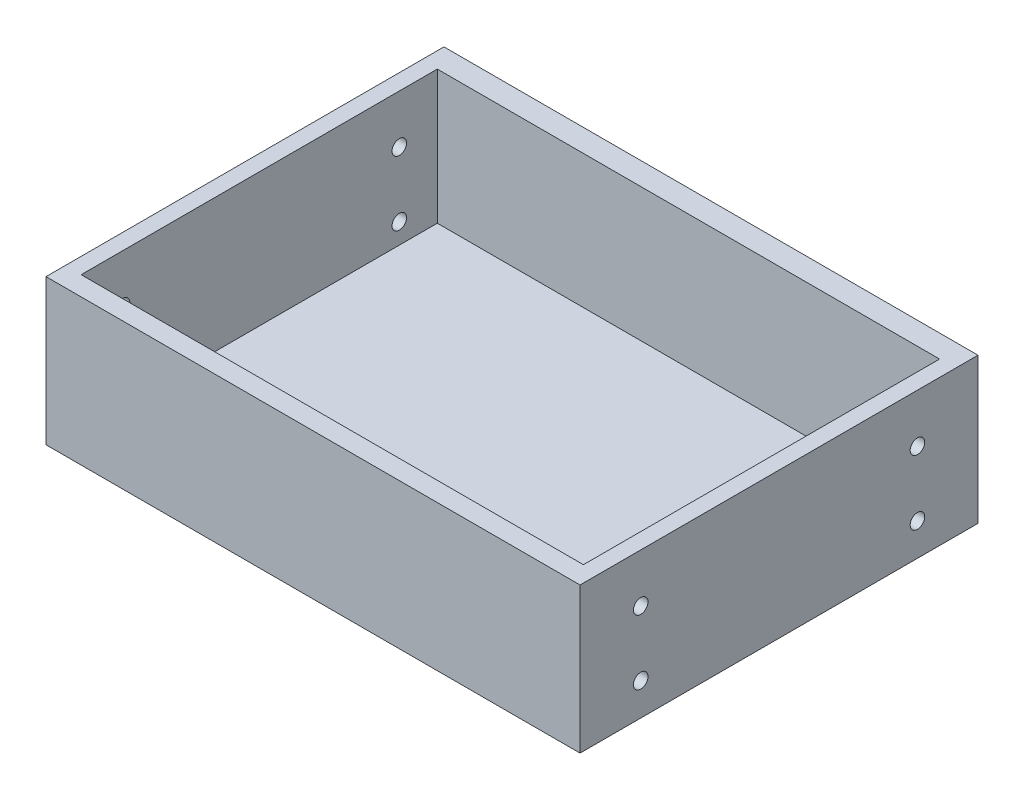
SolidWorks part; units mm, degrees
ref_plane "Front Plane" through (0, 0, 0) normal (0, 0, 1) x (1, 0, 0)
ref_plane "Top Plane" through (0, 0, 0) normal (0, 1, 0) x (1, 0, 0)
ref_plane "Right Plane" through (0, 0, 0) normal (1, 0, 0) x (0, 0, -1)
sketch "Sketch1" plane through (0, 0, 0) normal (0, 1, 0) x (1, 0, 0)
  line L1 (0, 0) -> (-440, 0)
  line L2 (0, 0) -> (0, 327.8893)
  line L3 (0, 327.8893) -> (-440, 327.8893)
  line L4 (-440, 0) -> (-440, 327.8893)
  dimension "D1" = 440
extrude "Boss-Extrude1" add sketch "Sketch1" along normal blind 120 contours L4 L1 L2 L3
sketch "Sketch8" plane through (0, 120, 0) normal (0, 1, 0) x (1, 0, 0)
  line L8 (-13.0805, 15.867) -> (-426.9088, 15.867)
  line L9 (-13.0805, 15.867) -> (-13.0805, 309.3089)
  line L10 (-13.0805, 309.3089) -> (-426.9088, 309.3089)
  line L11 (-426.9088, 15.867) -> (-426.9088, 309.3089)
  line L12 (-13.0805, 15.867) -> (-426.9088, 309.3089) construction
  line L13 (-13.0805, 309.3089) -> (-426.9088, 15.867) construction
  point P0 (-219.9946, 162.588)
extrude "Cut-Extrude1" cut sketch "Sketch8" against normal blind 110
sketch "Sketch9" plane through (-426.9088, 0, 0) normal (1, 0, 0) x (0, 0, -1)
  circle A0 centre (278, 80) radius 6
  circle A2 centre (278, 26.7196) radius 6
  circle A3 centre (50, 80) radius 6
  circle A4 centre (50, 26.7196) radius 6.0175
  point P8 (0, 0)
extrude "Cut-Extrude4" cut sketch "Sketch9" against normal blind 110 contours A0 | A2 | A3 | A4
sketch "Sketch10" plane through (0, 0, 0) normal (1, 0, 0) x (0, 0, -1)
  circle A0 centre (50, 80) radius 6
  circle A1 centre (50, 26.7196) radius 6.0175
  circle A2 centre (278, 26.7196) radius 6
  circle A3 centre (278, 80) radius 6
extrude "Cut-Extrude5" cut sketch "Sketch10" against normal blind 110 contours A0 | A2 | A1 | A3
